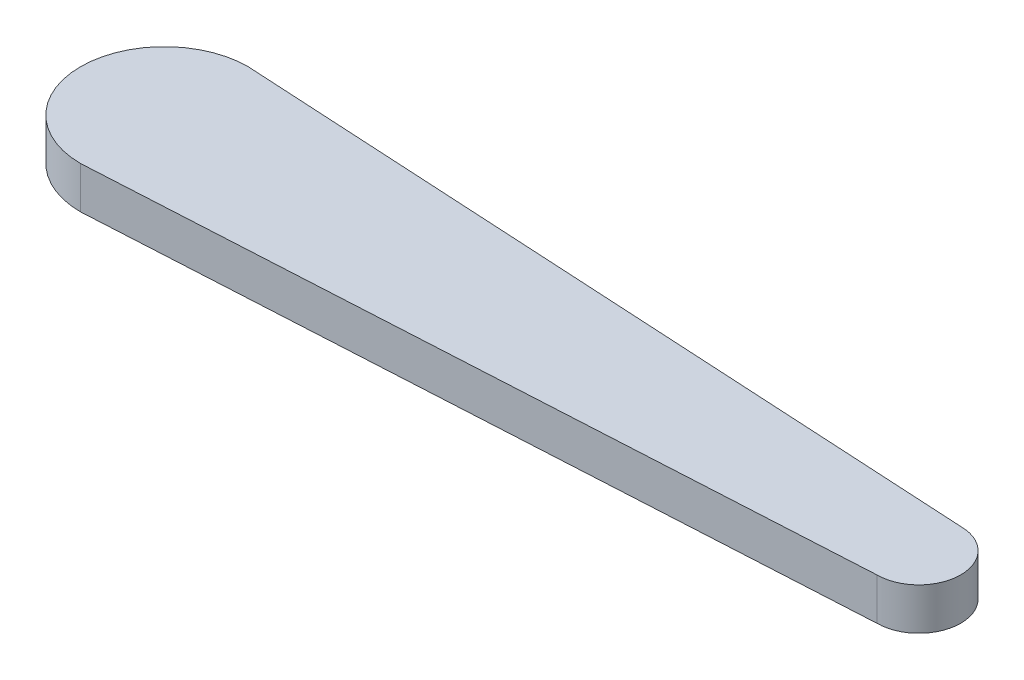
SolidWorks part; units mm, degrees
ref_plane "Front Plane" through (0, 0, 0) normal (0, 0, 1) x (1, 0, 0)
ref_plane "Top Plane" through (0, 0, 0) normal (0, 1, 0) x (1, 0, 0)
ref_plane "Right Plane" through (0, 0, 0) normal (1, 0, 0) x (0, 0, -1)
sketch "Sketch1" plane through (0, 0, 0) normal (0, 1, 0) x (1, 0, 0)
  line L0 (0, 10) -> (90, 5)
  line L1 (0, -10) -> (90, -5)
  arc A0 (0, 10) -> (0, -10) centre (0, 0) ccw
  arc A1 (90, -5) -> (90, 5) centre (90, 0) ccw
  dimension "D1" = 20
  dimension "D2" = 10
  dimension "D3" = 90
extrude "Boss-Extrude1" add sketch "Sketch1" along normal blind 5
